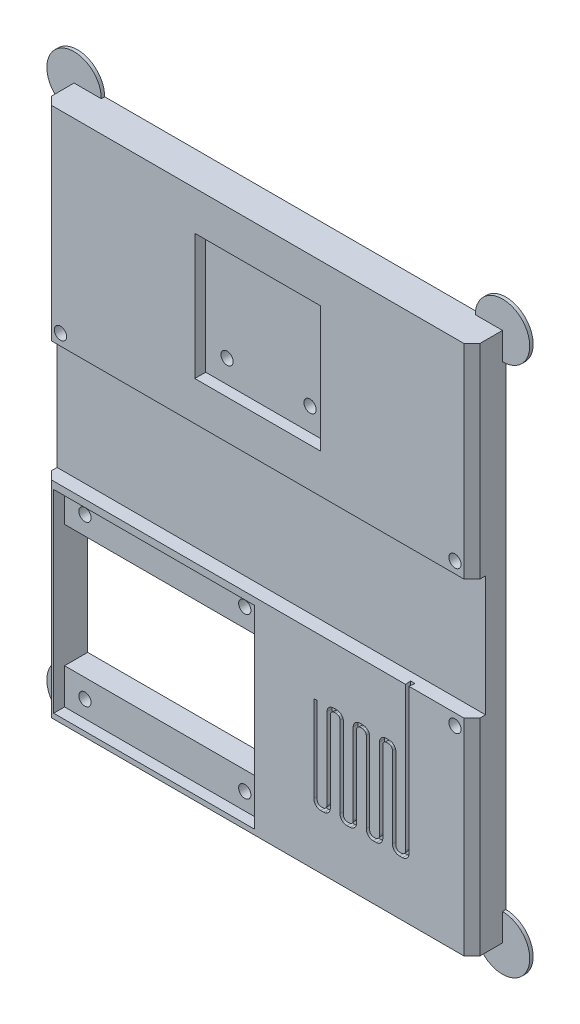
SolidWorks part; units mm, degrees
ref_plane "Front Plane" through (0, 0, 0) normal (0, 0, 1) x (1, 0, 0)
ref_plane "Top Plane" through (0, 0, 0) normal (0, 1, 0) x (1, 0, 0)
ref_plane "Right Plane" through (0, 0, 0) normal (1, 0, 0) x (0, 0, -1)
sketch "Sketch2" [suppressed] plane through (0, 0, 0) normal (0, 0, 1) x (1, 0, 0)
  line L0 (9.8069, 1.0971) -> (9.8069, -3.1704) construction
  line L1 (6.8551, -5.1618) -> (6.8551, -16.1618) construction
  line L2 (6.8551, -16.1618) -> (16.3814, -10.6618) construction
  line L3 (16.3814, -10.6618) -> (6.8551, -5.1618) construction
  line L4 (6.8551, -10.6618) -> (2.6647, -10.6618) construction
  line L5 (9.5069, 1.0971) -> (9.5069, -2.443)
  line L6 (6.5551, -6.3743) -> (6.5551, -9.8618)
  line L7 (8.0551, -15.8154) -> (15.4814, -11.5279)
  line L8 (15.4814, -9.7958) -> (8.0551, -5.5082)
  line L9 (6.0551, -10.3618) -> (3.5127, -10.3618)
  line L10 (10.1069, 1.0971) -> (10.1069, -2.3736)
  line L11 (7.1551, -6.5475) -> (7.1551, -14.7762)
  line L12 (7.9051, -15.2092) -> (15.0314, -11.0948)
  line L13 (15.0314, -10.2288) -> (7.9051, -6.1145)
  line L14 (6.0551, -10.9618) -> (3.5127, -10.9618)
  line L15 (9.5069, 1.0971) -> (9.5069, -3.1704) construction
  line L16 (10.1069, 1.0971) -> (10.1069, -3.1704) construction
  line L17 (6.8551, -10.9618) -> (2.6647, -10.9618) construction
  line L18 (6.8551, -10.3618) -> (2.6647, -10.3618) construction
  line L19 (6.5551, -11.4618) -> (6.5551, -14.9494)
  line L20 (6.5551, -4.6422) -> (6.5551, -16.6814) construction
  line L21 (7.1551, -15.6422) -> (15.7814, -10.6618) construction
  line L22 (15.7814, -10.6618) -> (7.1551, -5.6814) construction
  line L23 (7.1551, -5.6814) -> (7.1551, -15.6422) construction
  line L24 (6.5551, -16.6814) -> (16.9814, -10.6618) construction
  line L25 (16.9814, -10.6618) -> (6.5551, -4.6422) construction
  circle A0 centre (10.1647, -10.6618) radius 7.5 construction
  arc A1 (9.0767, -2.9381) -> (10.5803, -2.8729) centre (10.1647, -10.6618) ccw
  arc A2 (3.0162, -11.5215) -> (3.0162, -9.8021) centre (10.1647, -10.6618) ccw
  arc A3 (9.5069, 1.0971) -> (10.1069, 1.0971) centre (9.8069, 1.0971) cw
  circle A7 centre (10.1647, -10.6618) radius 7.8 construction
  circle A8 centre (10.1647, -10.6618) radius 7.2 construction
  arc A9 (10.1069, -2.3736) -> (10.5803, -2.8729) centre (10.6069, -2.3736) ccw
  arc A10 (9.5069, -2.443) -> (9.0767, -2.9381) centre (9.0069, -2.443) cw
  arc A11 (3.5127, -10.3618) -> (3.0162, -9.8021) centre (3.5127, -9.8618) cw
  arc A12 (3.5127, -10.9618) -> (3.0162, -11.5215) centre (3.5127, -11.4618) ccw
  arc A13 (6.0551, -10.3618) -> (6.5551, -9.8618) centre (6.0551, -9.8618) ccw
  arc A14 (6.5551, -11.4618) -> (6.0551, -10.9618) centre (6.0551, -11.4618) ccw
  arc A15 (15.0314, -11.0948) -> (15.0314, -10.2288) centre (14.7814, -10.6618) ccw
  arc A16 (7.1551, -14.7762) -> (7.9051, -15.2092) centre (7.6551, -14.7762) ccw
  arc A17 (7.1551, -6.5475) -> (7.9051, -6.1145) centre (7.6551, -6.5475) cw
  arc A18 (15.4814, -11.5279) -> (15.4814, -9.7958) centre (14.9814, -10.6618) ccw
  arc A19 (6.5551, -14.9494) -> (8.0551, -15.8154) centre (7.5551, -14.9494) ccw
  arc A20 (6.5551, -6.3743) -> (8.0551, -5.5082) centre (7.5551, -6.3743) cw
  point P12 (6.8551, -10.6618)
  dimension "D2" = 15
  dimension "D3" = 0.5
  dimension "D4" = 1
  dimension "D1" = 11
sketch "Sketch5" plane through (0, 0, 0) normal (0, 0, 1) x (1, 0, 0)
  line L1 (-31.5, 48) -> (31.5, 48)
  line L2 (-31.5, 48) -> (-31.5, -30)
  line L3 (-31.5, -30) -> (31.5, -30)
  line L4 (31.5, 48) -> (31.5, -30)
  point P4 (0, 48)
  dimension "D1" = 63
  dimension "D2" = 30
  dimension "D3" = 48
extrude "Boss-Extrude2" add sketch "Sketch5" along normal blind 5
sketch "Sketch1" plane through (0, 0, 5) normal (0, 0, 1) x (1, 0, 0)
  line L1 (-31, 17.6) -> (31, 17.6) construction
  line L2 (-31, 17.6) -> (-31, 0) construction
  line L3 (-31, 0) -> (31, 0) construction
  line L4 (31, 17.6) -> (31, 0) construction
  line L5 (-9.1, 41.514) -> (9.1, 41.514) construction
  line L6 (-9.1, 41.514) -> (-9.1, 24.114) construction
  line L7 (-9.1, 24.114) -> (9.1, 24.114) construction
  line L8 (9.1, 41.514) -> (9.1, 24.114) construction
  line L9 (-30.1379, -1.3413) -> (-1.1379, -1.3413) construction
  line L10 (-30.1379, -1.3413) -> (-30.1379, -28.8413) construction
  line L11 (-30.1379, -28.8413) -> (-1.1379, -28.8413) construction
  line L12 (-1.1379, -1.3413) -> (-1.1379, -28.8413) construction
  line L13 (-27.6379, -7.8413) -> (-3.6379, -7.8413) construction
  line L14 (-27.6379, -7.8413) -> (-27.6379, -22.8413) construction
  line L15 (-27.6379, -22.8413) -> (-3.6379, -22.8413) construction
  line L16 (-3.6379, -7.8413) -> (-3.6379, -22.8413) construction
  line L17 (0, 37.0153) -> (0, 31.2479) construction
  point P4 (0, 17.6)
  point P18 (0, 0)
  point P20 (-26.7166, -26.6413)
  point P21 (-3.2166, -26.6413)
  point P22 (-3.2166, -4.0013)
  point P23 (-26.7166, -3.1413)
  point P26 (6.1, 27.114)
  point P27 (0, 41.514)
  point P30 (-6.1, 27.114)
  point P32 (-15.6379, -7.8413)
  point P33 (-15.6379, -28.8413)
  dimension "D1" = 17.6
  dimension "D2" = 18.2
  dimension "D3" = 17.4
  dimension "D4" = 27.5
  dimension "D5" = 29
  dimension "D6" = 15
  dimension "D7" = 24
  dimension "D8" = 6
  dimension "D9" = 23.5
  dimension "D10" = 23.5
  dimension "D11" = 12.2
  dimension "D12" = 3
  dimension "D13" = 62
  dimension "D14" = 1.8
sketch "Pause" plane through (0, 0, 5) normal (0, 0, 1) x (1, 0, 0)
  line L0 (19.5, -1.8962) -> (19.5, -8.6557) construction
  line L1 (12.5, -10.5) -> (12.5, -19.5) construction
  line L2 (18.5, -10.5) -> (18.5, -19.5) construction
  line L3 (8, -15) -> (12.5, -15) construction
  line L4 (18.5, -15) -> (23, -15) construction
  line L5 (12.5, -10.5) -> (14.5, -10.5) construction
  line L6 (14.5, -10.5) -> (14.5, -19.5) construction
  line L7 (14.5, -19.5) -> (12.5, -19.5) construction
  line L8 (18.5, -10.5) -> (16.5, -10.5) construction
  line L9 (16.5, -10.5) -> (16.5, -19.5) construction
  line L10 (16.5, -19.5) -> (18.5, -19.5) construction
  line L11 (19.2, -1.8962) -> (19.2, -7.3417)
  line L12 (12.2, -10.9) -> (12.2, -14.2)
  line L13 (14.1, -19.8) -> (12.9, -19.8)
  line L14 (14.8, -10.9) -> (14.8, -19.1)
  line L15 (12.9, -10.2) -> (14.1, -10.2)
  line L16 (18.8, -10.9) -> (18.8, -14.2)
  line L17 (16.9, -19.8) -> (18.1, -19.8)
  line L18 (16.2, -10.9) -> (16.2, -19.1)
  line L19 (18.1, -10.2) -> (16.9, -10.2)
  line L20 (8, -15.3) -> (8.006, -15.3)
  line L21 (19.3, -15.3) -> (22.1521, -15.3)
  line L22 (19.8, -1.8962) -> (19.8, -8.2287)
  line L23 (12.8, -11.3) -> (12.8, -18.7)
  line L24 (13.7, -19.2) -> (13.3, -19.2)
  line L25 (14.2, -11.3) -> (14.2, -18.7)
  line L26 (13.3, -10.8) -> (13.7, -10.8)
  line L27 (18.2, -11.3) -> (18.2, -18.7)
  line L28 (17.3, -19.2) -> (17.7, -19.2)
  line L29 (16.8, -11.3) -> (16.8, -18.7)
  line L30 (17.7, -10.8) -> (17.3, -10.8)
  line L31 (8, -14.7) -> (8.006, -14.7)
  line L32 (19.3, -14.7) -> (22.1521, -14.7)
  line L33 (19.2, -1.8962) -> (19.2, -8.6557) construction
  line L34 (8.8479, -15.3) -> (11.7, -15.3)
  line L35 (19.8, -1.8962) -> (19.8, -8.6557) construction
  line L36 (8, -15.3) -> (12.5, -15.3) construction
  line L37 (8.8479, -14.7) -> (11.7, -14.7)
  line L38 (8, -14.7) -> (12.5, -14.7) construction
  line L39 (12.2, -15.8) -> (12.2, -19.1)
  line L40 (12.2, -10.2) -> (12.2, -19.8) construction
  line L41 (18.5, -14.7) -> (23, -14.7) construction
  line L42 (18.8, -15.8) -> (18.8, -19.1)
  line L43 (18.8, -10.2) -> (18.8, -19.8) construction
  line L44 (18.5, -15.3) -> (23, -15.3) construction
  line L45 (22.994, -14.7) -> (23, -14.7)
  line L46 (22.994, -15.3) -> (23, -15.3)
  line L47 (16.8, -19.2) -> (18.2, -19.2) construction
  line L48 (16.8, -10.8) -> (16.8, -19.2) construction
  line L49 (18.2, -10.8) -> (18.2, -19.2) construction
  line L50 (18.2, -10.8) -> (16.8, -10.8) construction
  line L51 (12.8, -10.8) -> (12.8, -19.2) construction
  line L52 (14.2, -19.2) -> (12.8, -19.2) construction
  line L53 (14.2, -10.8) -> (14.2, -19.2) construction
  line L54 (12.8, -10.8) -> (14.2, -10.8) construction
  line L55 (16.2, -10.2) -> (16.2, -19.8) construction
  line L56 (18.8, -10.2) -> (16.2, -10.2) construction
  line L57 (16.2, -19.8) -> (18.8, -19.8) construction
  line L58 (14.8, -19.8) -> (12.2, -19.8) construction
  line L59 (14.8, -10.2) -> (14.8, -19.8) construction
  line L60 (12.2, -10.2) -> (14.8, -10.2) construction
  line L61 (19.5, -1.8962) -> (19.5, -8.6557) construction
  line L62 (31.5, -30) -> (31.5, 48) construction
  line L64 (-31.5, -30) -> (31.5, -30) construction
  line L65 (19.8, -1.8962) -> (19.2, -1.8962)
  circle A0 centre (15.5, -15) radius 7.5 construction
  arc A2 (18.5072, -7.803) -> (20.0108, -8.6366) centre (15.5, -15) ccw
  arc A3 (8.3515, -15.8597) -> (22.6485, -15.8597) centre (15.5, -15) ccw
  circle A4 centre (15.5, -15) radius 7.8 construction
  circle A5 centre (15.5, -15) radius 7.2 construction
  arc A6 (22.6485, -14.1403) -> (8.3515, -14.1403) centre (15.5, -15) ccw
  arc A7 (19.2, -7.3417) -> (18.5072, -7.803) centre (18.7, -7.3417) cw
  arc A8 (20.0108, -8.6366) -> (19.8, -8.2287) centre (20.3, -8.2287) cw
  arc A9 (8.8479, -15.3) -> (8.3515, -15.8597) centre (8.8479, -15.8) ccw
  arc A10 (8.8479, -14.7) -> (8.3515, -14.1403) centre (8.8479, -14.2) cw
  arc A11 (22.1521, -14.7) -> (22.6485, -14.1403) centre (22.1521, -14.2) ccw
  arc A12 (22.6485, -15.8597) -> (22.1521, -15.3) centre (22.1521, -15.8) ccw
  arc A13 (19.3, -14.7) -> (18.8, -14.2) centre (19.3, -14.2) cw
  arc A14 (19.3, -15.3) -> (18.8, -15.8) centre (19.3, -15.8) ccw
  arc A15 (12.2, -15.8) -> (11.7, -15.3) centre (11.7, -15.8) ccw
  arc A16 (11.7, -14.7) -> (12.2, -14.2) centre (11.7, -14.2) ccw
  arc A17 (17.3, -19.2) -> (16.8, -18.7) centre (17.3, -18.7) cw
  arc A18 (18.2, -18.7) -> (17.7, -19.2) centre (17.7, -18.7) cw
  arc A19 (18.2, -11.3) -> (17.7, -10.8) centre (17.7, -11.3) ccw
  arc A20 (16.8, -11.3) -> (17.3, -10.8) centre (17.3, -11.3) cw
  arc A21 (12.8, -18.7) -> (13.3, -19.2) centre (13.3, -18.7) ccw
  arc A22 (13.7, -19.2) -> (14.2, -18.7) centre (13.7, -18.7) ccw
  arc A23 (14.2, -11.3) -> (13.7, -10.8) centre (13.7, -11.3) ccw
  arc A24 (12.8, -11.3) -> (13.3, -10.8) centre (13.3, -11.3) cw
  arc A25 (16.2, -10.9) -> (16.9, -10.2) centre (16.9, -10.9) cw
  arc A26 (18.8, -10.9) -> (18.1, -10.2) centre (18.1, -10.9) ccw
  arc A27 (18.8, -19.1) -> (18.1, -19.8) centre (18.1, -19.1) cw
  arc A28 (16.9, -19.8) -> (16.2, -19.1) centre (16.9, -19.1) cw
  arc A29 (12.2, -19.1) -> (12.9, -19.8) centre (12.9, -19.1) ccw
  arc A30 (14.1, -19.8) -> (14.8, -19.1) centre (14.1, -19.1) ccw
  arc A31 (14.8, -10.9) -> (14.1, -10.2) centre (14.1, -10.9) ccw
  arc A32 (12.2, -10.9) -> (12.9, -10.2) centre (12.9, -10.9) cw
  point P18 (12.5, -15)
  point P73 (22.6937, -14.7)
  dimension "D5" = 15
  dimension "D6" = 0.5
  dimension "D7" = 0.7
  dimension "D1" = 2
  dimension "D2" = 2
  dimension "D3" = 2
  dimension "D4" = 9
  dimension "D8" = 12
  dimension "D9" = 16
  dimension "D10" = 15
  dimension "D11" = 0.3
  dimension "D12" = 0.3
extrude "Cut-Extrude1" [suppressed] cut sketch "Pause" against normal blind 2
sketch "Teensy" plane through (0, 0, 5) normal (0, 0, 1) x (1, 0, 0)
  line L0 (-31.5, 48) -> (-31.5, -30) construction
  line L1 (-31.5, 18) -> (31.5, 18)
  line L2 (-31.5, 18) -> (-31.5, 0.3)
  line L3 (-31.5, 0.3) -> (31.5, 0.3)
  line L4 (31.5, 18) -> (31.5, 0.3)
  line L5 (31.5, -30) -> (31.5, 48) construction
  line L6 (31.5, 48) -> (-31.5, 48) construction
  dimension "D1" = 17.7
  dimension "D2" = 30
extrude "Cut-Extrude3" cut sketch "Teensy" against normal blind 2
sketch "Sketch7" plane through (0, 0, 5) normal (0, 0, 1) x (1, 0, 0)
  line L1 (-9.25, 42.25) -> (9.25, 42.25)
  line L2 (-9.25, 42.25) -> (-9.25, 23.75)
  line L3 (-9.25, 23.75) -> (9.25, 23.75)
  line L4 (9.25, 42.25) -> (9.25, 23.75)
  line L5 (31.5, 48) -> (-31.5, 48) construction
  point P4 (0, 42.25)
  point P5 (-9.25, 33)
  dimension "D1" = 18.5
  dimension "D2" = 18.5
  dimension "D3" = 15
extrude "Cut-Extrude4" cut sketch "Sketch7" against normal blind 1.6
sketch "Sketch8" plane through (0, 0, 5) normal (0, 0, 1) x (1, 0, 0)
  line L0 (-31.5, -30) -> (31.5, -30) construction
  line L1 (-30, -0.75) -> (-0.5, -0.75)
  line L2 (-30, -0.75) -> (-30, -29.25)
  line L3 (-30, -29.25) -> (-0.5, -29.25)
  line L4 (-0.5, -0.75) -> (-0.5, -29.25)
  line L5 (-31.5, 0.3) -> (-31.5, -30) construction
  point P4 (-30, -15)
  dimension "D1" = 29.5
  dimension "D2" = 28.5
  dimension "D3" = 15
  dimension "D4" = 1.5
extrude "Cut-Extrude5" cut sketch "Sketch8" against normal blind 1.6
sketch "Sketch9" plane through (0, 0, 3.4) normal (0, 0, 1) x (1, 0, 0)
  line L0 (-30, -0.75) -> (-30, -29.25) construction
  line L1 (-30, -6) -> (-1, -6)
  line L2 (-30, -6) -> (-30, -24)
  line L3 (-30, -24) -> (-1, -24)
  line L4 (-1, -6) -> (-1, -24)
  line L5 (-0.5, -0.75) -> (-30, -0.75) construction
  line L6 (-15.25, -0.75) -> (-15.25, -29.25) construction
  line L7 (-18.021, -15) -> (-12.479, -15) construction
  line L8 (-30, -29.25) -> (-0.5, -29.25) construction
  line L10 (31.5012, 9.15) -> (28.925, 9.15) construction
  line L11 (31.5, 0.3) -> (31.5, 18) construction
  line L13 (0, 0) -> (0, 11.9396) construction
  circle A0 centre (-27, -3.25) radius 0.9
  circle A1 centre (-3.5, -3.25) radius 0.9
  circle A2 centre (-3.5, -26.75) radius 0.9
  circle A3 centre (-27, -26.75) radius 0.9
  circle A4 centre (-6.1, 27.114) radius 0.9
  circle A5 centre (6.1, 27.114) radius 0.9
  circle A6 centre (-29, 19.65) radius 0.9
  circle A7 centre (29, 19.65) radius 0.9
  circle A8 centre (29, -1.35) radius 0.9
  circle A9 centre (29, 19.65) radius 1.75 construction
  point P23 (-15.25, -15)
  point P37 (31.5, 9.15)
  dimension "D4" = 1.8
  dimension "D8" = 3.5
  dimension "D1" = 29
  dimension "D2" = 18
  dimension "D3" = 21
  dimension "D5" = 23.5
  dimension "D6" = 23.5
  dimension "D7" = 58
extrude "Cut-Extrude6" cut sketch "Sketch9" against normal through all and the other way through all
sketch "Sketch10" plane through (0, 0, 0) normal (0, 0, -1) x (-1, 0, 0)
  circle A0 centre (31.5, 48) radius 4
  circle A1 centre (-31.5, 48) radius 4
  circle A2 centre (-31.5, -30) radius 4
  circle A3 centre (31.5, -30) radius 4
  dimension "D1" = 8
extrude "Boss-Extrude3" add sketch "Sketch10" against normal blind 0.5
sketch "Sketch11" plane through (0, 0, 5) normal (0, 0, 1) x (1, 0, 0)
  line L0 (-31.5, 48) -> (-31.5, 18) construction
  line L1 (-28.5, 42) -> (-28.1, 42)
  line L2 (-28.5, 42) -> (-28.5, 12)
  line L3 (-28.5, 12) -> (-28.1, 12)
  line L4 (-28.1, 42) -> (-28.1, 12)
  line L5 (-25.5, 42) -> (-24.9, 42)
  line L6 (-25.5, 42) -> (-25.5, 12)
  line L7 (-25.5, 12) -> (-24.9, 12)
  line L8 (-24.9, 42) -> (-24.9, 12)
  line L9 (-22.5, 42) -> (-21.7, 42)
  line L10 (-22.5, 42) -> (-22.5, 12)
  line L11 (-22.5, 12) -> (-21.7, 12)
  line L12 (-21.7, 42) -> (-21.7, 12)
  line L13 (31.5, 48) -> (-31.5, 48) construction
  dimension "D1" = 30
  dimension "D2" = 3
  dimension "D3" = 3
  dimension "D4" = 3
  dimension "D5" = 0.4
  dimension "D6" = 0.6
  dimension "D7" = 0.8
  dimension "D8" = 6
extrude "Cut-Extrude7" [suppressed] cut sketch "Sketch11" against normal blind 2 draft 5
chamfer "Chamfer2" distance 1.2 angle 45 4 edges at (-31.5, -14.85, 5) (31.5, -14.85, 5) (31.5, 33, 5) (-31.5, 33, 5)
sketch "Sketch12" plane through (0, 0, 5) normal (0, 0, 1) x (1, 0, 0)
  line L0 (22, 0.3) -> (22, -21.75) construction
  line L1 (22, -21.75) -> (20.0714, -21.75) construction
  line L2 (20.0714, -21.75) -> (20.0714, -8.25) construction
  line L3 (20.0714, -8.25) -> (18.1429, -8.25) construction
  line L4 (18.1429, -8.25) -> (18.1429, -21.75) construction
  line L5 (18.1429, -21.75) -> (16.2143, -21.75) construction
  line L6 (16.2143, -21.75) -> (16.2143, -8.25) construction
  line L7 (16.2143, -8.25) -> (14.2857, -8.25) construction
  line L8 (14.2857, -8.25) -> (14.2857, -21.75) construction
  line L9 (14.2857, -21.75) -> (12.3571, -21.75) construction
  line L10 (12.3571, -21.75) -> (12.3571, -8.25) construction
  line L11 (12.3571, -8.25) -> (10.4286, -8.25) construction
  line L12 (10.4286, -8.25) -> (10.4286, -21.75) construction
  line L13 (10.4286, -21.75) -> (8.5, -21.75) construction
  line L14 (21.75, 0.3) -> (21.75, -20.9)
  line L15 (21.15, -21.5) -> (20.9214, -21.5)
  line L16 (20.3214, -20.9) -> (20.3214, -9)
  line L17 (19.3214, -8) -> (18.8929, -8)
  line L18 (8.5, -21.75) -> (8.5, -8.25) construction
  line L19 (31.5, -26) -> (31.5, 44) construction
  line L20 (-27.5, -30) -> (27.5, -30) construction
  line L21 (-31.5, 0.3) -> (31.5, 0.3) construction
  line L22 (17.8929, -9) -> (17.8929, -20.9)
  line L23 (17.2929, -21.5) -> (17.0643, -21.5)
  line L24 (16.4643, -20.9) -> (16.4643, -9)
  line L25 (15.4643, -8) -> (15.0357, -8)
  line L26 (14.0357, -9) -> (14.0357, -20.9)
  line L27 (13.4357, -21.5) -> (13.2071, -21.5)
  line L28 (12.6071, -20.9) -> (12.6071, -9)
  line L29 (11.6071, -8) -> (11.1786, -8)
  line L30 (10.1786, -9) -> (10.1786, -20.9)
  line L31 (9.5786, -21.5) -> (9.35, -21.5)
  line L32 (8.75, -20.9) -> (8.75, -8.25)
  line L33 (22.25, 0.3) -> (22.25, -21)
  line L34 (21.25, -22) -> (20.8214, -22)
  line L35 (19.8214, -21) -> (19.8214, -9.1)
  line L36 (19.2214, -8.5) -> (18.9929, -8.5)
  line L37 (18.3929, -9.1) -> (18.3929, -21)
  line L38 (17.3929, -22) -> (16.9643, -22)
  line L39 (15.9643, -21) -> (15.9643, -9.1)
  line L40 (15.3643, -8.5) -> (15.1357, -8.5)
  line L41 (14.5357, -9.1) -> (14.5357, -21)
  line L42 (13.5357, -22) -> (13.1071, -22)
  line L43 (12.1071, -21) -> (12.1071, -9.1)
  line L44 (11.5071, -8.5) -> (11.2786, -8.5)
  line L45 (10.6786, -9.1) -> (10.6786, -21)
  line L46 (9.6786, -22) -> (9.25, -22)
  line L47 (8.25, -21) -> (8.25, -8.25)
  line L48 (21.75, 0.3) -> (22.25, 0.3)
  line L49 (8.75, -8.25) -> (8.25, -8.25)
  line L50 (14.0357, -21.5) -> (12.6071, -21.5) construction
  line L51 (12.6071, -21.5) -> (12.6071, -8) construction
  line L52 (14.0357, -8) -> (14.0357, -21.5) construction
  line L53 (17.8929, -21.5) -> (16.4643, -21.5) construction
  line L54 (16.4643, -21.5) -> (16.4643, -8) construction
  line L55 (17.8929, -8) -> (17.8929, -21.5) construction
  line L56 (21.75, -21.5) -> (20.3214, -21.5) construction
  line L57 (20.3214, -21.5) -> (20.3214, -8) construction
  line L58 (21.75, 0.3) -> (21.75, -21.5) construction
  line L59 (19.8214, -22) -> (19.8214, -8.5) construction
  line L60 (19.8214, -8.5) -> (18.3929, -8.5) construction
  line L61 (18.3929, -8.5) -> (18.3929, -22) construction
  line L62 (15.9643, -22) -> (15.9643, -8.5) construction
  line L63 (15.9643, -8.5) -> (14.5357, -8.5) construction
  line L64 (14.5357, -8.5) -> (14.5357, -22) construction
  line L65 (12.1071, -22) -> (12.1071, -8.5) construction
  line L66 (12.1071, -8.5) -> (10.6786, -8.5) construction
  line L67 (10.6786, -8.5) -> (10.6786, -22) construction
  line L68 (10.1786, -8) -> (10.1786, -21.5) construction
  line L69 (10.1786, -21.5) -> (8.75, -21.5) construction
  line L70 (8.75, -21.5) -> (8.75, -8.25) construction
  line L71 (12.6071, -8) -> (10.1786, -8) construction
  line L72 (16.4643, -8) -> (14.0357, -8) construction
  line L73 (20.3214, -8) -> (17.8929, -8) construction
  line L74 (22.25, 0.3) -> (22.25, -22) construction
  line L75 (22.25, -22) -> (19.8214, -22) construction
  line L76 (18.3929, -22) -> (15.9643, -22) construction
  line L77 (14.5357, -22) -> (12.1071, -22) construction
  line L78 (10.6786, -22) -> (8.25, -22) construction
  line L79 (8.25, -22) -> (8.25, -8.25) construction
  arc A0 (13.2071, -21.5) -> (12.6071, -20.9) centre (13.2071, -20.9) cw
  arc A1 (14.0357, -20.9) -> (13.4357, -21.5) centre (13.4357, -20.9) cw
  arc A2 (17.0643, -21.5) -> (16.4643, -20.9) centre (17.0643, -20.9) cw
  arc A3 (17.8929, -20.9) -> (17.2929, -21.5) centre (17.2929, -20.9) cw
  arc A4 (20.9214, -21.5) -> (20.3214, -20.9) centre (20.9214, -20.9) cw
  arc A5 (21.75, -20.9) -> (21.15, -21.5) centre (21.15, -20.9) cw
  arc A6 (19.8214, -9.1) -> (19.2214, -8.5) centre (19.2214, -9.1) ccw
  arc A7 (18.9929, -8.5) -> (18.3929, -9.1) centre (18.9929, -9.1) ccw
  arc A8 (15.9643, -9.1) -> (15.3643, -8.5) centre (15.3643, -9.1) ccw
  arc A9 (15.1357, -8.5) -> (14.5357, -9.1) centre (15.1357, -9.1) ccw
  arc A10 (12.1071, -9.1) -> (11.5071, -8.5) centre (11.5071, -9.1) ccw
  arc A11 (11.2786, -8.5) -> (10.6786, -9.1) centre (11.2786, -9.1) ccw
  arc A12 (10.1786, -20.9) -> (9.5786, -21.5) centre (9.5786, -20.9) cw
  arc A13 (9.35, -21.5) -> (8.75, -20.9) centre (9.35, -20.9) cw
  arc A14 (11.1786, -8) -> (10.1786, -9) centre (11.1786, -9) ccw
  arc A15 (12.6071, -9) -> (11.6071, -8) centre (11.6071, -9) ccw
  arc A16 (15.0357, -8) -> (14.0357, -9) centre (15.0357, -9) ccw
  arc A17 (16.4643, -9) -> (15.4643, -8) centre (15.4643, -9) ccw
  arc A18 (18.8929, -8) -> (17.8929, -9) centre (18.8929, -9) ccw
  arc A19 (20.3214, -9) -> (19.3214, -8) centre (19.3214, -9) ccw
  arc A20 (22.25, -21) -> (21.25, -22) centre (21.25, -21) cw
  arc A21 (20.8214, -22) -> (19.8214, -21) centre (20.8214, -21) cw
  arc A22 (18.3929, -21) -> (17.3929, -22) centre (17.3929, -21) cw
  arc A23 (16.9643, -22) -> (15.9643, -21) centre (16.9643, -21) cw
  arc A24 (14.5357, -21) -> (13.5357, -22) centre (13.5357, -21) cw
  arc A25 (13.1071, -22) -> (12.1071, -21) centre (13.1071, -21) cw
  arc A26 (10.6786, -21) -> (9.6786, -22) centre (9.6786, -21) cw
  arc A27 (9.25, -22) -> (8.25, -21) centre (9.25, -21) cw
  point P22 (8.5, -15)
  dimension "D5" = 0.6
  dimension "D6" = 1
  dimension "D1" = 13.5
  dimension "D2" = 13.5
  dimension "D3" = 9.5
  dimension "D4" = 15
  dimension "D7" = 0.25
  dimension "D8" = 0.25
extrude "Cut-Extrude8" cut sketch "Sketch12" against normal blind 0.8 draft 5 draft outward yes
sketch "Sketch13" plane through (0, 0, 5) normal (0, 0, 1) x (1, 0, 0)
  line L0 (8.75, -8.25) -> (8.25, -8.25) construction
  circle A0 centre (8.5172, -8.25) radius 0.5
  dimension "D1" = 1
extrude "Cut-Extrude9" [suppressed] cut sketch "Sketch13" against normal through all
